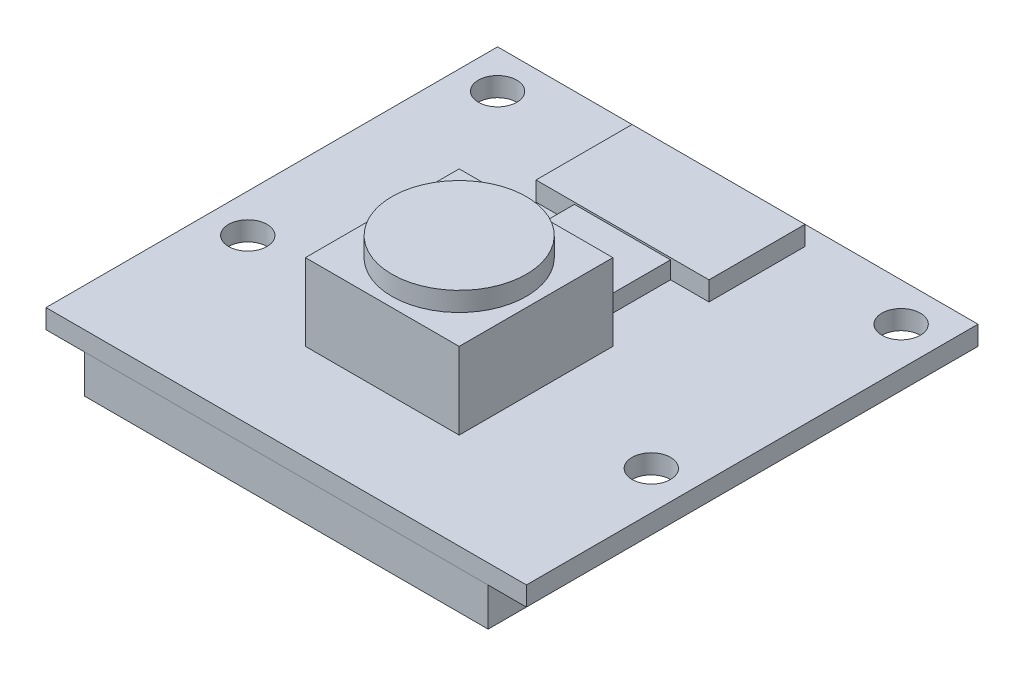
SolidWorks part; units mm, degrees
ref_plane "Front Plane" through (0, 0, 0) normal (0, 0, 1) x (1, 0, 0)
ref_plane "Top Plane" through (0, 0, 0) normal (0, 1, 0) x (1, 0, 0)
ref_plane "Right Plane" through (0, 0, 0) normal (1, 0, 0) x (0, 0, -1)
sketch "Sketch1" plane through (0, 0, 0) normal (0, 1, 0) x (1, 0, 0)
  line L1 (-12.5, 11.75) -> (12.5, 11.75)
  line L2 (-12.5, 11.75) -> (-12.5, -11.75)
  line L3 (-12.5, -11.75) -> (12.5, -11.75)
  line L4 (12.5, 11.75) -> (12.5, -11.75)
  line L5 (-12.5, 11.75) -> (12.5, -11.75) construction
  line L6 (-12.5, -11.75) -> (12.5, 11.75) construction
  point P1 (0, 0)
  dimension "D1" = 25
  dimension "D2" = 23.5
extrude "Boss-Extrude1" add sketch "Sketch1" along normal blind 1
sketch "Sketch2" plane through (0, 1, 0) normal (0, 1, 0) x (1, 0, 0)
  line L0 (12.5, 11.75) -> (-12.5, 11.75) construction
  line L1 (-12.5, 11.75) -> (-12.5, -11.75) construction
  line L2 (12.5, -11.75) -> (12.5, 11.75) construction
  circle A0 centre (-10.5, 9.75) radius 1
  circle A1 centre (10.5, 9.75) radius 1
  circle A2 centre (10.5, -3.25) radius 1
  circle A3 centre (-10.5, -3.25) radius 1
  dimension "D1" = 2
  dimension "D4" = 2
  dimension "D7" = 2
  dimension "D9" = 2
  dimension "D12" = 2
  dimension "D2" = 2
  dimension "D3" = 2
  dimension "D5" = 2
  dimension "D6" = 2
  dimension "D8" = 13
  dimension "D10" = 2
  dimension "D11" = 13
extrude "Cut-Extrude1" cut sketch "Sketch2" against normal blind 1
sketch "Sketch3" plane through (0, 1, 0) normal (0, 1, 0) x (1, 0, 0)
  line L0 (12.5, -11.75) -> (12.5, 11.75) construction
  line L1 (-4.5, 10.75) -> (4.5, 10.75)
  line L2 (-4.5, 10.75) -> (-4.5, 5.75)
  line L3 (-4.5, 5.75) -> (4.5, 5.75)
  line L4 (4.5, 10.75) -> (4.5, 5.75)
  line L5 (-4.5, 10.75) -> (4.5, 5.75) construction
  line L6 (-4.5, 5.75) -> (4.5, 10.75) construction
  line L7 (-12.5, 11.75) -> (-12.5, -11.75) construction
  line L8 (12.5, 11.75) -> (-12.5, 11.75) construction
  point P0 (0, 8.25)
  dimension "D1" = 8
  dimension "D2" = 8
  dimension "D3" = 1
  dimension "D4" = 5
extrude "Boss-Extrude2" add sketch "Sketch3" along normal blind 1
sketch "Sketch4" plane through (0, 1, 0) normal (0, 1, 0) x (1, 0, 0)
  line L0 (-12.5, 11.75) -> (-12.5, -11.75) construction
  line L1 (-2.5, 5.75) -> (2.5, 5.75)
  line L2 (-2.5, 5.75) -> (-2.5, 1.25)
  line L3 (-2.5, 1.25) -> (2.5, 1.25)
  line L4 (2.5, 5.75) -> (2.5, 1.25)
  line L5 (-2.5, 5.75) -> (2.5, 1.25) construction
  line L6 (-2.5, 1.25) -> (2.5, 5.75) construction
  line L7 (12.5, -11.75) -> (12.5, 11.75) construction
  line L8 (-4.5, 5.75) -> (4.5, 5.75) construction
  point P0 (0, 3.5)
  dimension "D1" = 10
  dimension "D2" = 10
  dimension "D3" = 0
  dimension "D4" = 4.5
extrude "Boss-Extrude3" add sketch "Sketch4" along normal blind 0.9
sketch "Sketch5" plane through (0, 1, 0) normal (0, 1, 0) x (1, 0, 0)
  line L0 (-12.5, 11.75) -> (-12.5, -11.75) construction
  line L1 (-4, 1.25) -> (4, 1.25)
  line L2 (-4, 1.25) -> (-4, -6.75)
  line L3 (-4, -6.75) -> (4, -6.75)
  line L4 (4, 1.25) -> (4, -6.75)
  line L5 (-4, 1.25) -> (4, -6.75) construction
  line L6 (-4, -6.75) -> (4, 1.25) construction
  line L7 (12.5, -11.75) -> (12.5, 11.75) construction
  line L8 (-12.5, -11.75) -> (12.5, -11.75) construction
  point P0 (0, -2.75)
  dimension "D1" = 8
  dimension "D2" = 8
  dimension "D3" = 8.5
  dimension "D4" = 8.5
  dimension "D5" = 5
extrude "Boss-Extrude4" add sketch "Sketch5" along normal blind 4
sketch "Sketch6" plane through (0, 5, 0) normal (0, 1, 0) x (1, 0, 0)
  line L0 (-4, 1.25) -> (-4, -6.75) construction
  line L1 (-4, -6.75) -> (4, -6.75) construction
  circle A0 centre (0, -2.75) radius 3.5
  dimension "D1" = 7
  dimension "D3" = 4
  dimension "D2" = 4
extrude "Boss-Extrude5" add sketch "Sketch6" along normal blind 1
sketch "Sketch8" plane through (0, 0, 0) normal (0, -1, 0) x (1, 0, 0)
  line L0 (-12.5, -11.75) -> (-12.5, 11.75) construction
  line L1 (-10.5, 11.74) -> (10.5, 11.74)
  line L2 (-10.5, 11.74) -> (-10.5, 6.74)
  line L3 (-10.5, 6.74) -> (10.5, 6.74)
  line L4 (10.5, 11.74) -> (10.5, 6.74)
  line L5 (-10.5, 11.74) -> (10.5, 6.74) construction
  line L6 (-10.5, 6.74) -> (10.5, 11.74) construction
  line L7 (12.5, 11.75) -> (12.5, -11.75) construction
  line L8 (-12.5, 11.75) -> (12.5, 11.75) construction
  point P0 (0, 9.24)
  dimension "D1" = 2
  dimension "D2" = 2
  dimension "D3" = 5
  dimension "D4" = 0.01
extrude "Boss-Extrude6" add sketch "Sketch8" along normal blind 2
